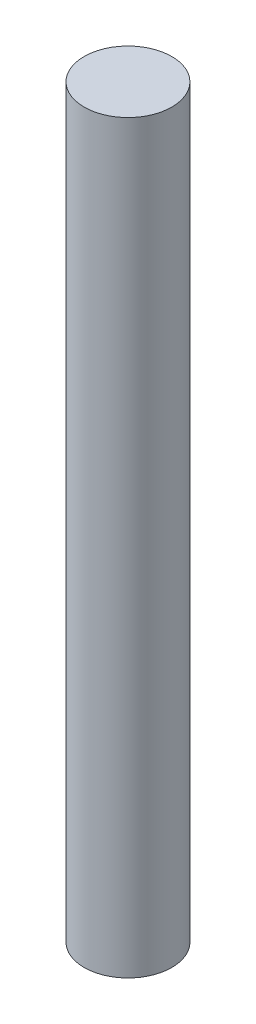
SolidWorks part; units mm, degrees
ref_plane "Front Plane" through (0, 0, 0) normal (0, 0, 1) x (1, 0, 0)
ref_plane "Top Plane" through (0, 0, 0) normal (0, 1, 0) x (1, 0, 0)
ref_plane "Right Plane" through (0, 0, 0) normal (1, 0, 0) x (0, 0, -1)
sketch "Sketch1" plane through (0, 0, 0) normal (0, 1, 0) x (1, 0, 0)
  circle A0 centre (0, 0) radius 2
  dimension "D1" = 4
extrude "Boss-Extrude1" add sketch "Sketch1" along normal blind 34
